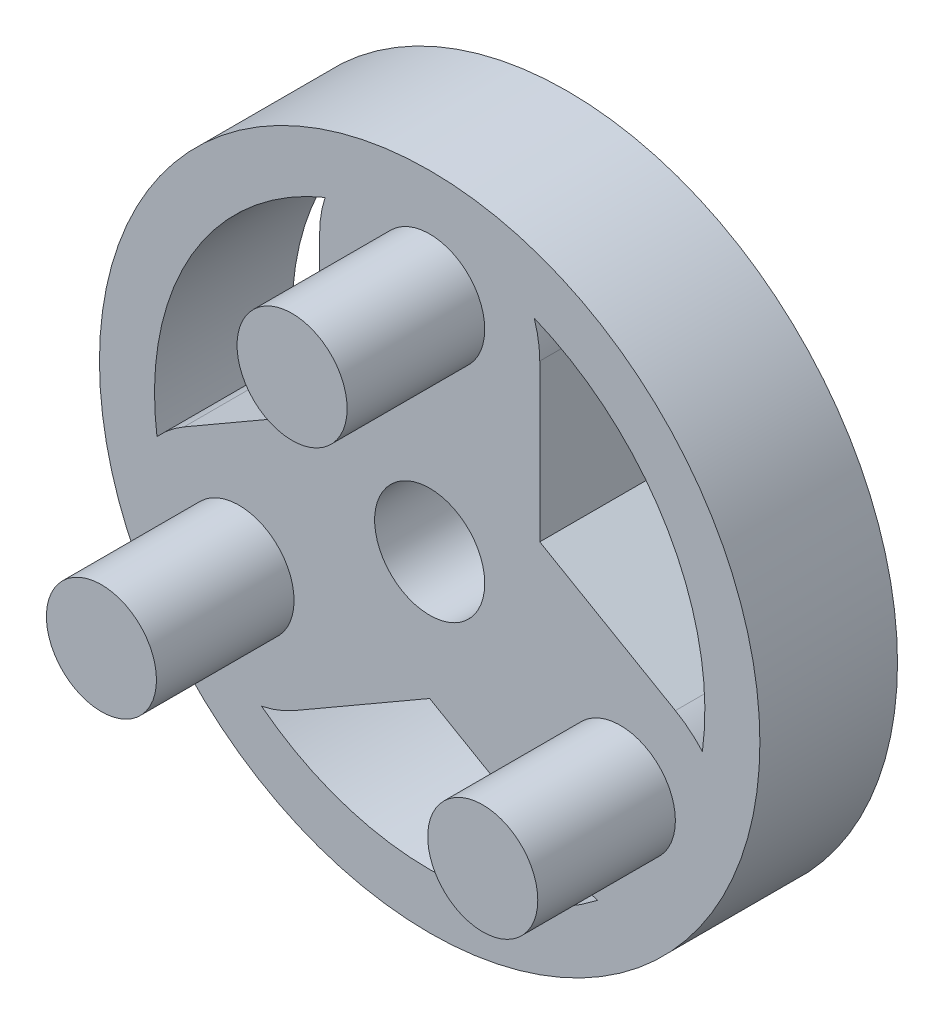
SolidWorks part; units mm, degrees
ref_plane "Front Plane" through (0, 0, 0) normal (0, 0, 1) x (1, 0, 0)
ref_plane "Top Plane" through (0, 0, 0) normal (0, 1, 0) x (1, 0, 0)
ref_plane "Right Plane" through (0, 0, 0) normal (1, 0, 0) x (0, 0, -1)
sketch "Sketch1" plane through (0, 0, 0) normal (0, 0, 1) x (1, 0, 0)
  line L0 (0, 0) -> (0, 8) construction
  line L1 (0, 0) -> (6.9282, -4) construction
  line L2 (0, 0) -> (-6.9282, -4) construction
  line L3 (4, 2.3094) -> (4, 8)
  line L4 (-4, 2.3094) -> (-8.9282, -0.5359)
  line L5 (0, -4.6188) -> (4.9282, -7.4641)
  line L6 (-4, 2.3094) -> (-4, 8)
  line L7 (0, -4.6188) -> (-4.9282, -7.4641)
  line L8 (4, 2.3094) -> (8.9282, -0.5359)
  line L9 (-2, 3.4641) -> (-8.9282, -0.5359) construction
  line L10 (-4, 0) -> (-4, 8) construction
  line L11 (2, -3.4641) -> (-4.9282, -7.4641) construction
  line L12 (-2, -3.4641) -> (4.9282, -7.4641) construction
  line L13 (2, 3.4641) -> (8.9282, -0.5359) construction
  line L14 (4, 0) -> (4, 8) construction
  arc A0 (4, 8) -> (-4, 8) centre (0, 8) ccw
  arc A1 (4.9282, -7.4641) -> (8.9282, -0.5359) centre (6.9282, -4) ccw
  arc A2 (-8.9282, -0.5359) -> (-4.9282, -7.4641) centre (-6.9282, -4) ccw
  dimension "D1" = 120
  dimension "D2" = 120
  dimension "D3" = 8
  dimension "D4" = 8
  dimension "D5" = 8
  dimension "D7" = 4
extrude "Boss-Extrude1" add sketch "Sketch1" along normal blind 5
sketch "Sketch3" plane through (0, 0, 5) normal (0, 0, 1) x (1, 0, 0)
  circle A0 centre (0, 8) radius 2
  circle A1 centre (6.9282, -4) radius 2
  circle A2 centre (-6.9282, -4) radius 2
  circle A3 centre (0, 0) radius 2
  dimension "D1" = 4
  dimension "D2" = 4
extrude "Boss-Extrude2" add sketch "Sketch3" along normal blind 5
sketch "Sketch4" plane through (0, 0, 5) normal (0, 0, 1) x (1, 0, 0)
  circle A0 centre (0, 0) radius 2
extrude "Cut-Extrude1" cut sketch "Sketch4" against normal through all both and the other way through all
sketch "Sketch5" plane through (0, 0, 5) normal (0, 0, 1) x (1, 0, 0)
  circle A0 centre (0, 0) radius 12
  circle A1 centre (0, 0) radius 10
  dimension "D1" = 24
  dimension "D2" = 2
extrude "Boss-Extrude3" add sketch "Sketch5" against normal up to surface (5 mm away) up to face at (2, 0, 0)
